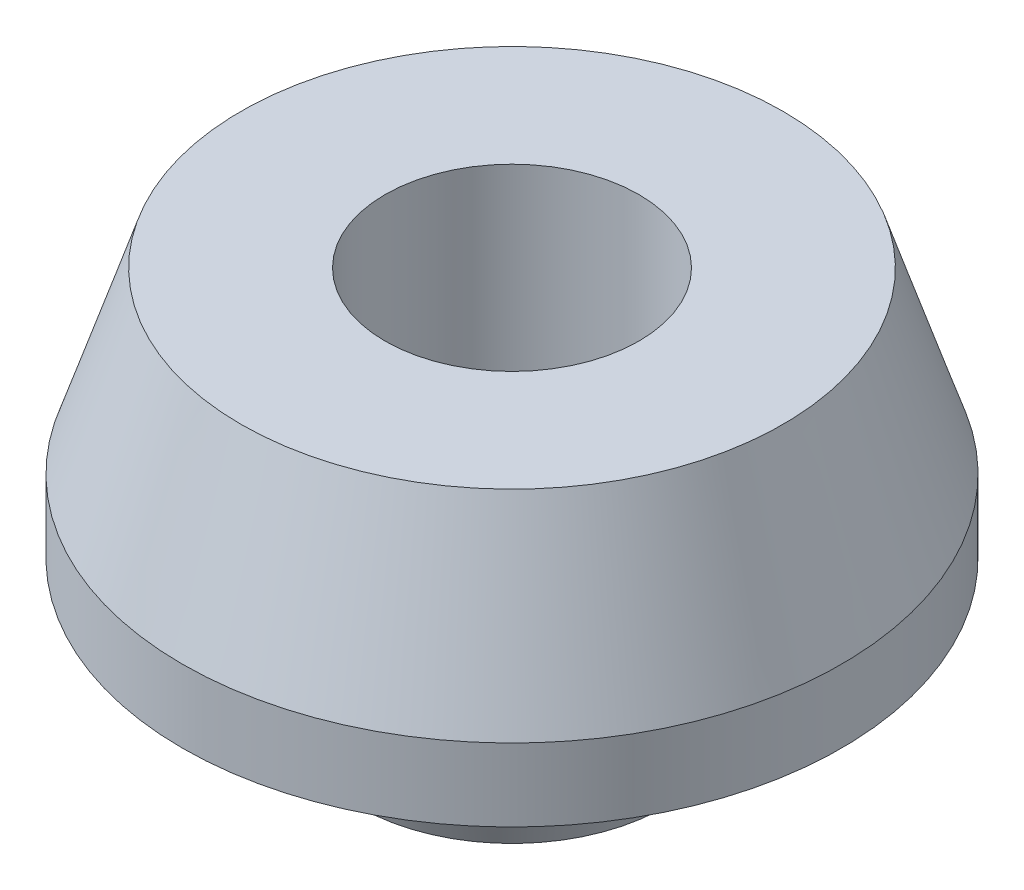
SolidWorks part; units mm, degrees
ref_plane "Front Plane" through (0, 0, 0) normal (0, 0, 1) x (1, 0, 0)
ref_plane "Top Plane" through (0, 0, 0) normal (0, 1, 0) x (1, 0, 0)
ref_plane "Right Plane" through (0, 0, 0) normal (1, 0, 0) x (0, 0, -1)
sketch "Sketch2" plane through (0, 0, 0) normal (0, 0, 1) x (1, 0, 0)
  line L0 (4.8, 0) -> (4.8, 14.75)
  line L1 (4.8, 14.75) -> (10.25, 14.75)
  line L2 (10.25, 14.75) -> (12.4608, 8)
  line L3 (12.4608, 8) -> (12.4608, 5.25)
  line L4 (12.4608, 5.25) -> (7.7108, 5.25)
  line L5 (7.7108, 5.25) -> (5.8, 0)
  line L6 (5.8, 0) -> (4.8, 0)
  line L7 (0, 0) -> (0, 14.75) construction
  dimension "D1" = 1
  dimension "D2" = 4.8
  dimension "D3" = 5.45
  dimension "D4" = 4.75
  dimension "D5" = 2.75
  dimension "D6" = 9.5
  dimension "D7" = 14.75
  dimension "D8" = 110
revolve "Revolve1" add sketch "Sketch2" angle 360 about L7
